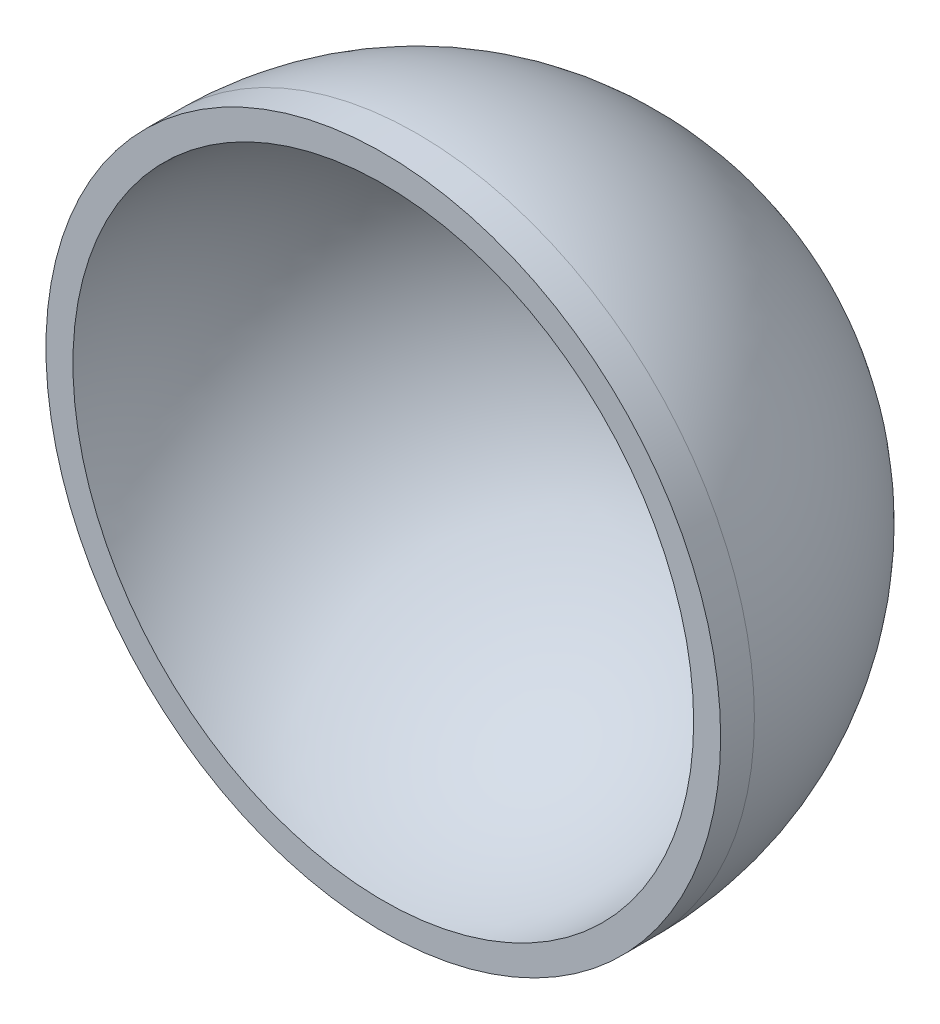
SolidWorks part; units mm, degrees
ref_plane "Front Plane" through (0, 0, 0) normal (0, 0, 1) x (1, 0, 0)
ref_plane "Top Plane" through (0, 0, 0) normal (0, 1, 0) x (1, 0, 0)
ref_plane "Right Plane" through (0, 0, 0) normal (1, 0, 0) x (0, 0, -1)
sketch "Sketch1" plane through (0, 0, 0) normal (0, 0, 1) x (1, 0, 0)
  circle A0 centre (0, 0) radius 50
  dimension "D1" = 100
extrude "Boss-Extrude1" add sketch "Sketch1" against normal blind 5 contours A0
sketch "Sketch2" plane through (0, 0, -5) normal (0, 0, -1) x (-1, 0, 0)
  line L0 (0, -50) -> (0, 50)
  circle A0 centre (0, 0) radius 50 construction
  arc A1 (0, 50) -> (0, -50) centre (0, 0) cw
  dimension "D1" = 100
revolve "Revolve1" add sketch "Sketch2" angle 180 about L0
sketch "Sketch4" plane through (0, 0, 0) normal (0, 0, 1) x (1, 0, 0)
  line L0 (0, -46) -> (0, 46)
  circle A0 centre (0, 0) radius 50 construction
  arc A1 (0, 46) -> (0, -46) centre (0, 0) cw
  dimension "D1" = 46
  dimension "D2" = 46
revolve "Cut-Revolve1" cut sketch "Sketch4" angle 360 about L0
sketch "Sketch5" plane through (0, 0, 0) normal (0, 1, 0) x (1, 0, 0)
  line L0 (0, -13.121) -> (0, 68.9318) construction
sketch "Sketch6" plane through (0, 0, 0) normal (0, 0, 1) x (1, 0, 0)
  line L0 (-88.418, 0) -> (95.7567, 0) construction
